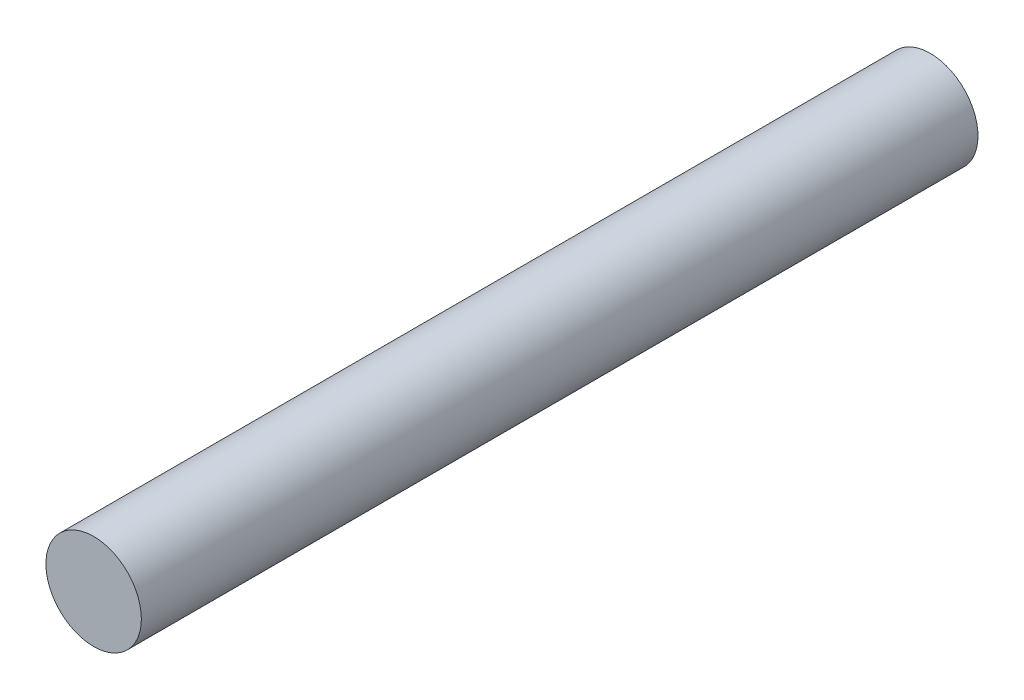
SolidWorks part; units mm, degrees
ref_plane "Alzado" through (0, 0, 0) normal (0, 0, 1) x (1, 0, 0)
ref_plane "Planta" through (0, 0, 0) normal (0, 1, 0) x (1, 0, 0)
ref_plane "Vista lateral" through (0, 0, 0) normal (1, 0, 0) x (0, 0, -1)
sketch "Croquis1" plane through (0, 0, 0) normal (0, 0, 1) x (1, 0, 0)
  circle A0 centre (0, 0) radius 8.5
extrude "Saliente-Extruir1" add sketch "Croquis1" along normal blind 149
